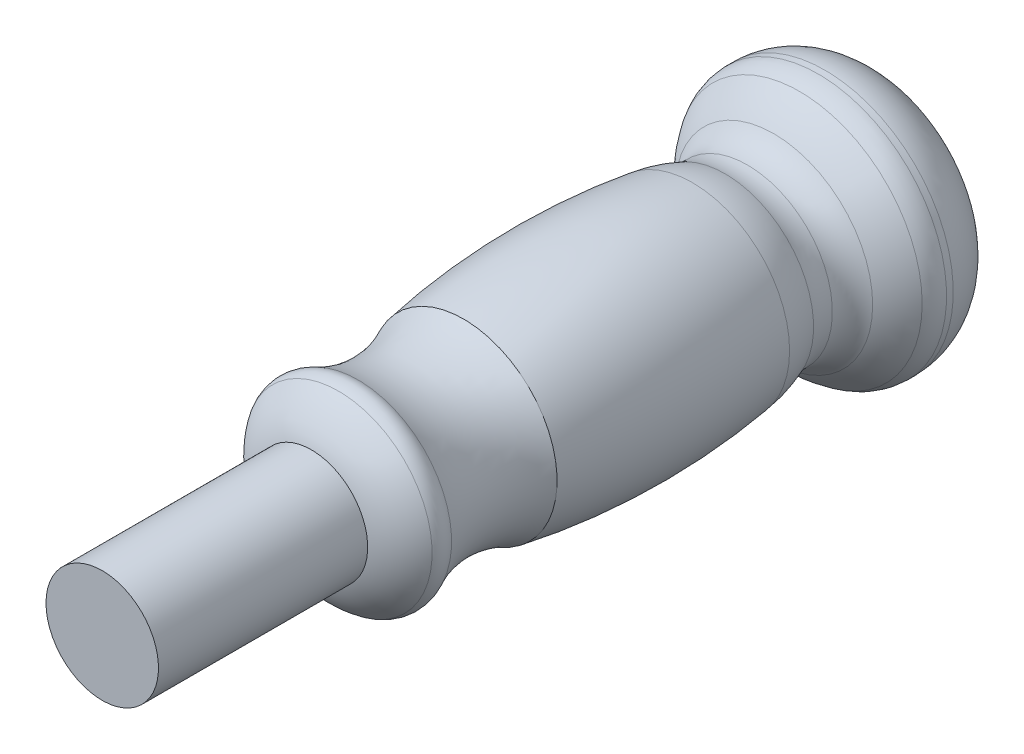
SolidWorks part; units mm, degrees
ref_plane "Front Plane" through (0, 0, 0) normal (0, 0, 1) x (1, 0, 0)
ref_plane "Top Plane" through (0, 0, 0) normal (0, 1, 0) x (1, 0, 0)
ref_plane "Right Plane" through (0, 0, 0) normal (1, 0, 0) x (0, 0, -1)
sketch "Sketch1" plane through (0, 0, 0) normal (0, 1, 0) x (1, 0, 0)
  line L0 (-10.922, 0) -> (0, 0)
  line L1 (-10.922, 0) -> (-10.922, 40.64)
  line L3 (0, 152.4) -> (0, 0)
  line L4 (0, 152.4) -> (-14.6482, 152.4)
  line L6 (-24.9064, 140.392) -> (-24.9064, 139.098)
  arc A0 (-10.922, 40.64) -> (-18.1463, 45.927) centre (-6.8859, 53.7343) cw
  arc A1 (-14.6482, 152.4) -> (-24.9064, 140.392) centre (-12.2105, 139.9318) ccw
  arc A2 (-18.1463, 49.7155) -> (-18.1463, 45.927) centre (-15.0439, 47.8212) ccw
  arc A3 (-16.4916, 125.3288) -> (-17.1792, 120.9917) centre (-26.6157, 124.7107) cw
  arc A4 (-18.1463, 49.7155) -> (-18.1463, 70.1995) centre (-39.1448, 59.9575) ccw
  arc A5 (-23.8226, 135.4378) -> (-19.2065, 130.4397) centre (-6.9494, 146.3907) ccw
  arc A6 (-18.8457, 114.664) -> (-18.1463, 70.1995) centre (123.4649, 94.6646) ccw
  arc A7 (-24.9064, 139.098) -> (-23.8226, 135.4378) centre (-18.1841, 139.098) ccw
  arc A8 (-17.1792, 120.9917) -> (-18.8457, 114.664) centre (8.6982, 110.7932) ccw
  arc A9 (-16.4916, 125.3288) -> (-19.2065, 130.4397) centre (-23.4607, 124.9033) ccw
  dimension "D1" = 111.76
  dimension "D2" = 10.922
  dimension "D3" = 40.64
revolve "Revolve5" add sketch "Sketch1" angle 360 about L3
